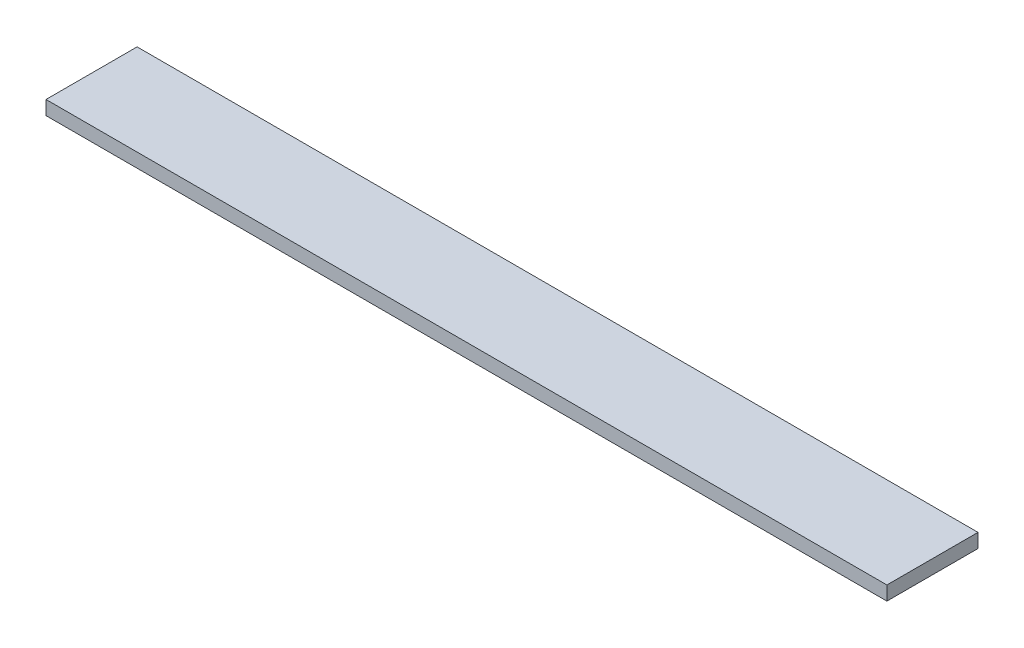
SolidWorks part; units mm, degrees
ref_plane "Front Plane" through (0, 0, 0) normal (0, 0, 1) x (1, 0, 0)
ref_plane "Top Plane" through (0, 0, 0) normal (0, 1, 0) x (1, 0, 0)
ref_plane "Right Plane" through (0, 0, 0) normal (1, 0, 0) x (0, 0, -1)
sketch "Sketch2" plane through (0, 0, 0) normal (0, 1, 0) x (1, 0, 0)
  line L1 (-93.2215, 49.4558) -> (668.7785, 49.4558)
  line L2 (-93.2215, 49.4558) -> (-93.2215, -33.0942)
  line L3 (-93.2215, -33.0942) -> (668.7785, -33.0942)
  line L4 (668.7785, 49.4558) -> (668.7785, -33.0942)
  dimension "D1" = 82.55
  dimension "D2" = 762
extrude "Boss-Extrude1" add sketch "Sketch2" along normal blind 12.7
